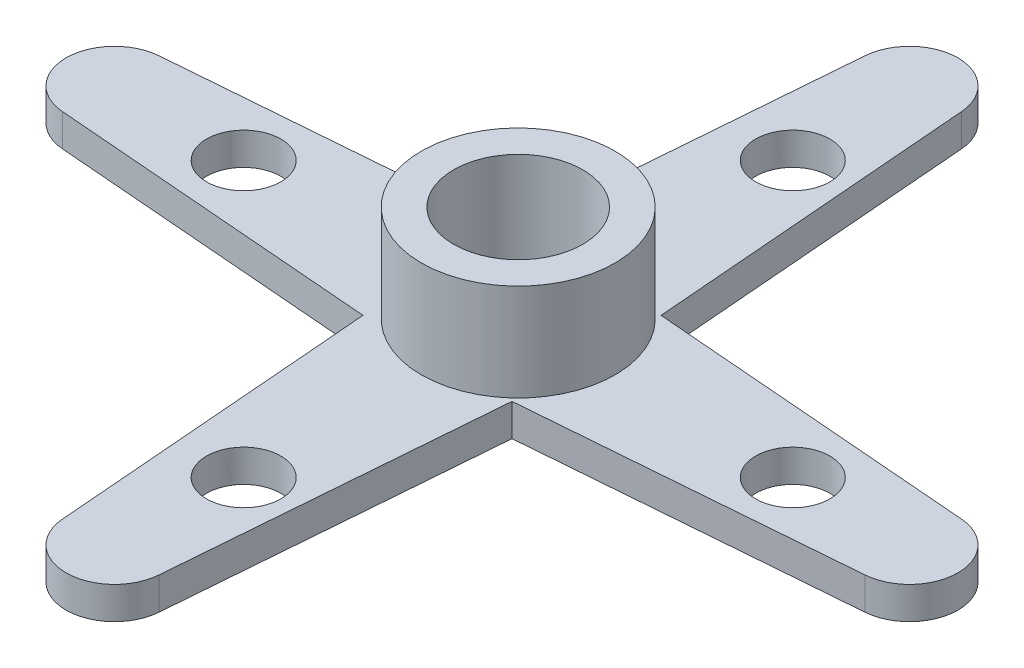
SolidWorks part; units mm, degrees
material "uhlíková ocel 7850"
ref_plane "Přední rovina" through (0, 0, 0) normal (0, 0, 1) x (1, 0, 0)
ref_plane "Horní rovina" through (0, 0, 0) normal (0, 1, 0) x (1, 0, 0)
ref_plane "Pravá rovina" through (0, 0, 0) normal (1, 0, 0) x (0, 0, -1)
sketch "Skica1" plane through (0, 0, 0) normal (0, 1, 0) x (1, 0, 0)
  line L0 (0, 0) -> (-12.5, 0) construction
  line L1 (-12.62, 1.4952) -> (-2.5, 2.3074)
  line L2 (0, 15.429) -> (0, 0) construction
  line L3 (-12.5, 0) -> (-39.2821, 0) construction
  line L6 (-12.62, -1.4952) -> (-2.5, -2.3074)
  line L7 (0, 2.5) -> (-5.8693, 2.5) construction
  line L8 (1.3026, 12.4274) -> (2.1148, 2.3074)
  line L9 (-1.6878, 12.4274) -> (-2.5, 2.3074)
  line L12 (12.2348, -1.4952) -> (2.1148, -2.3074)
  line L13 (12.2348, 1.4952) -> (2.1148, 2.3074)
  line L16 (-1.6878, -12.4274) -> (-2.5, -2.3074)
  line L17 (1.3026, -12.4274) -> (2.1148, -2.3074)
  circle A0 centre (0, 0) radius 2
  arc A1 (1.3026, 12.4274) -> (-1.6878, 12.4274) centre (-0.1926, 12.3074) ccw
  arc A2 (-12.62, 1.4952) -> (-12.62, -1.4952) centre (-12.5, 0) ccw
  arc A5 (12.2348, -1.4952) -> (12.2348, 1.4952) centre (12.1148, 0) ccw
  arc A7 (-1.6878, -12.4274) -> (1.3026, -12.4274) centre (-0.1926, -12.3074) ccw
  point P19 (0, 7.75)
  point P50 (-0.1926, 0)
  dimension "D1" = 4
  dimension "D2" = 1.5
  dimension "D3" = 2.5
  dimension "D5" = 15.5
  dimension "D4" = 12.5
  dimension "D6" = 4
extrude "Přidat vysunutím1" add sketch "Skica1" along normal blind 1
sketch "Skica2" plane through (0, 1, 0) normal (0, 1, 0) x (1, 0, 0)
  line L0 (-8.5, 0) -> (0, 0) construction
  line L1 (0, 0) -> (0, -4.2214) construction
  line L2 (0, 0) -> (8.5, 0) construction
  circle A0 centre (-8.5, 0) radius 1.15
  circle A1 centre (8.5, 0) radius 1.15
  dimension "D1" = 2.3
  dimension "D2" = 17
extrude "Odebrat vysunutím1" cut sketch "Skica2" against normal blind 2
sketch "Skica3" plane through (0, 1, 0) normal (0, 1, 0) x (1, 0, 0)
  circle A1 centre (0, 0) radius 3
  circle A2 centre (0, 0) radius 2
  circle A3 centre (0, 0) radius 2 construction
  dimension "D1" = 6
extrude "Přidat vysunutím2" add sketch "Skica3" along normal blind 3
pattern_circular "Kruhové pole1" count 4 over 360 about axis through (0, 0, 0) along (0, 1, 0) of "Odebrat vysunutím1"
